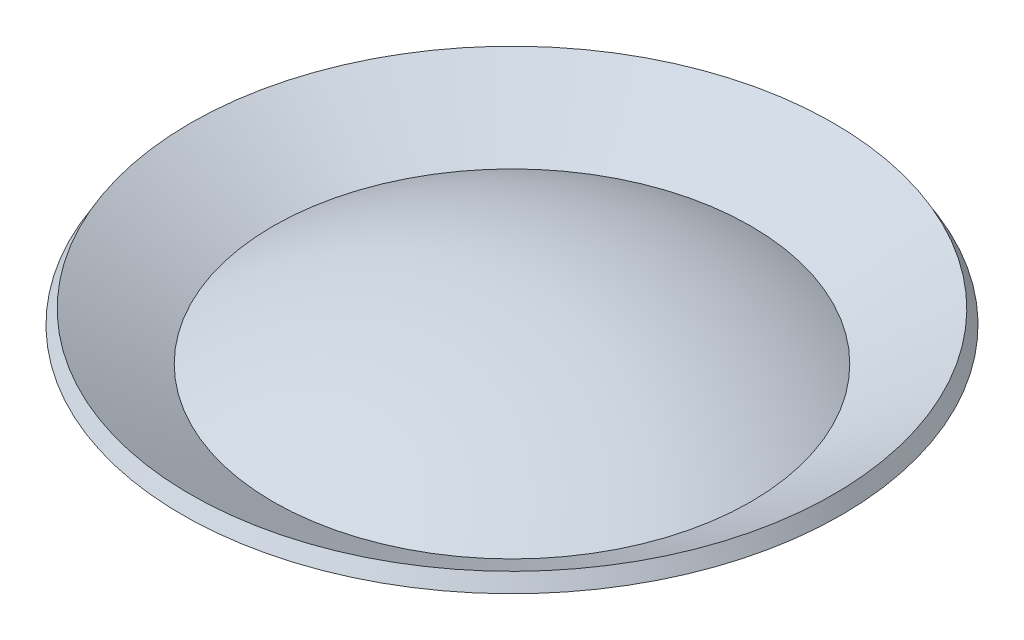
SolidWorks part; units mm, degrees
ref_plane "Ebene1" through (0, 0, 0) normal (0, 0, 1) x (1, 0, 0)
ref_plane "Ebene2" through (0, 0, 0) normal (0, 1, 0) x (1, 0, 0)
ref_plane "Ebene3" through (0, 0, 0) normal (1, 0, 0) x (0, 0, -1)
sketch "Skizze1" plane through (0, 0, 0) normal (0, 0, 1) x (1, 0, 0)
  line L1 (0, 0) -> (0, -30) construction
  line L2 (15, -4.0192) -> (20.1962, -1.0192)
  line L3 (14.9943, -5.1772) -> (20.6962, -1.8853)
  line L4 (20.1962, -1.0192) -> (20.6962, -1.8853)
  line L5 (0, 0) -> (0, -1)
  arc A0 (0, 0) -> (15, -4.0192) centre (0, -30) cw
  arc A1 (0, -1) -> (14.9943, -5.1772) centre (0, -30) cw
  point P1 (25.3702, -4.7962)
  dimension "D2" = 30
  dimension "D1" = 60
  dimension "D3" = 30
  dimension "D4" = 6
  dimension "D5" = 1
revolve "Rotation1" add sketch "Skizze1" angle 360 about L1
